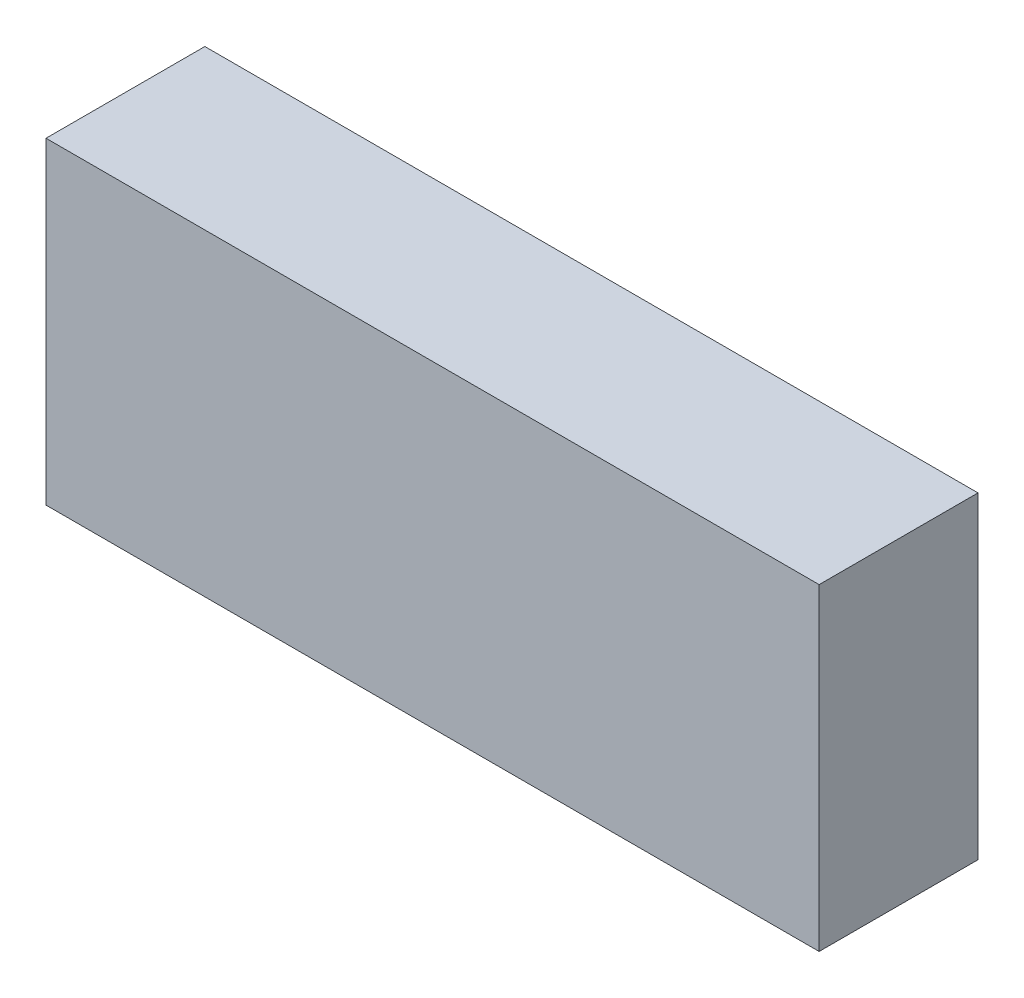
SolidWorks part; units mm, degrees
ref_plane "Front" through (0, 0, 0) normal (0, 0, 1) x (1, 0, 0)
ref_plane "Top" through (0, 0, 0) normal (0, 1, 0) x (1, 0, 0)
ref_plane "Right" through (0, 0, 0) normal (1, 0, 0) x (0, 0, -1)
sketch "Sketch1" plane through (0, 0, 0) normal (0, 0, 1) x (1, 0, 0)
  line L1 (0, 0) -> (73, 0)
  line L2 (0, 0) -> (0, 30)
  line L3 (0, 30) -> (73, 30)
  line L4 (73, 0) -> (73, 30)
  dimension "D1" = 73
  dimension "D2" = 30
extrude "Boss-Extrude1" add sketch "Sketch1" along normal blind 15
